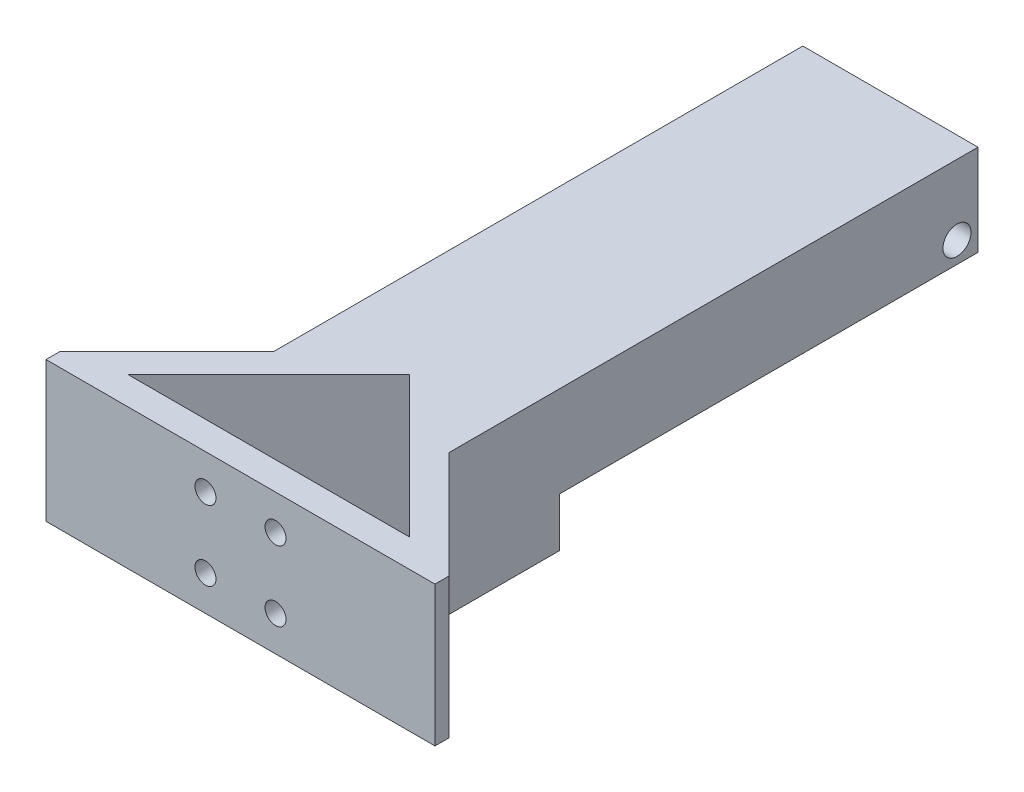
SolidWorks part; units mm, degrees
material "PLA"
ref_plane "정면" through (0, 0, 0) normal (0, 0, 1) x (1, 0, 0)
ref_plane "윗면" through (0, 0, 0) normal (0, 1, 0) x (1, 0, 0)
ref_plane "우측면" through (0, 0, 0) normal (1, 0, 0) x (0, 0, -1)
sketch "스케치1" plane through (0, 0, 0) normal (0, 1, 0) x (1, 0, 0)
  line L0 (27.75, 94.3974) -> (27.75, -27.5062) construction
  line L1 (40.2477, 92.7323) -> (15.2523, 92.7323)
  line L2 (0, 2) -> (0, 0)
  line L3 (15.2523, 17.2523) -> (0, 2)
  line L4 (40.2477, 92.7323) -> (40.2477, 17.2523)
  line L5 (40.2477, 17.2523) -> (55.5, 2)
  line L6 (55.5, 2) -> (55.5, 0)
  line L7 (55.5, 0) -> (0, 0)
  line L8 (15.2523, 92.7323) -> (15.2523, 17.2523)
  line L9 (27.75, 24.0931) -> (47.8431, 4)
  line L10 (47.8431, 4) -> (7.6569, 4)
  line L11 (7.6569, 4) -> (27.75, 24.0931)
  point P12 (27.75, 92.7323)
  point P18 (27.75, 5)
  dimension "D9" = 4
  dimension "D8" = 4
  dimension "D1" = 55.5
  dimension "D2" = 135
  dimension "D3" = 2
  dimension "D4" = 21.57
  dimension "D5" = 75.48
  dimension "D6" = 12.4977
  dimension "D7" = 4
extrude "보스-돌출1" add sketch "스케치1" along normal blind 20
sketch "스케치2" plane through (0, 0, 0) normal (0, 0, 1) x (1, 0, 0)
  line L0 (0, 20) -> (0, 0) construction
  line L2 (0, 10) -> (60.2338, 10) construction
  line L3 (27.75, 23.0111) -> (27.75, -4.7654) construction
  circle A1 centre (22.75, 15) radius 1.5
  circle A2 centre (32.75, 15) radius 1.5
  circle A5 centre (32.75, 5) radius 1.5
  circle A6 centre (22.75, 5) radius 1.5
  dimension "D5" = 3
extrude "컷-돌출1" cut sketch "스케치2" against normal blind 5
ref_plane "평면1" through (15.25, 0, 0) normal (1, 0, 0) x (0, 0, -1)
sketch "스케치4" plane through (0, 0, 0) normal (0, -1, 0) x (1, 0, 0)
  line L0 (15.25, -11) -> (15.25, 11) construction
  line L1 (40.2477, -92.7323) -> (15.25, -92.7323)
  line L2 (40.2477, -92.7323) -> (40.2477, -33.0023)
  line L3 (40.2477, -33.0023) -> (15.25, -33.0023)
  line L4 (15.25, -92.7323) -> (15.25, -33.0023)
  dimension "D1" = 59.73
extrude "컷-돌출3" cut sketch "스케치4" against normal blind 7
ref_plane "평면7" through (15.2523, 0, 0) normal (-1, 0, 0) x (0, 0, 1)
sketch "스케치8" plane through (15.2523, 0, 0) normal (-1, 0, 0) x (0, 0, 1)
  line L0 (-92.7323, 20) -> (-92.7323, 7) construction
  line L1 (-33.0023, 7) -> (-92.7323, 7) construction
  circle A0 centre (-89.7323, 10) radius 2
  dimension "D3" = 4
  dimension "D1" = 3
  dimension "D2" = 3
extrude "컷-돌출5" cut sketch "스케치8" against normal through all
